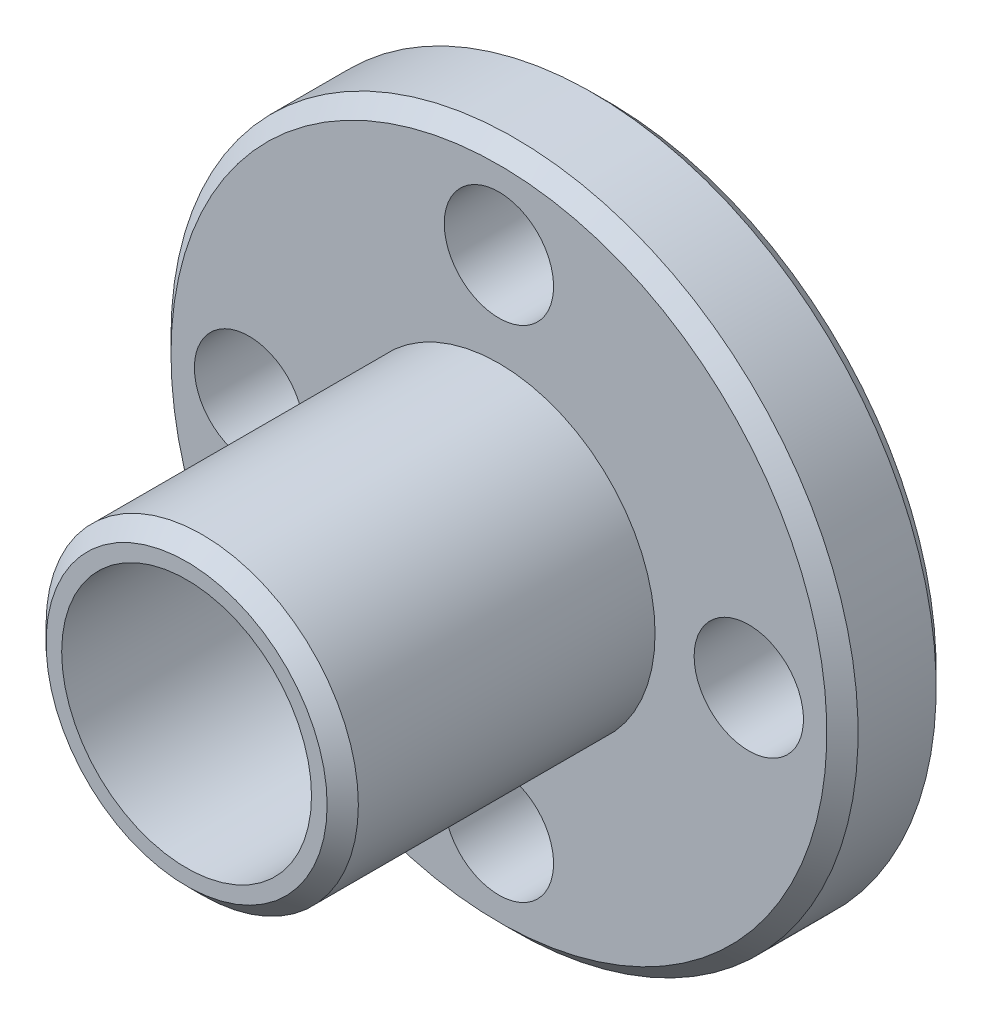
SolidWorks part; units mm, degrees
ref_plane "前视基准面" through (0, 0, 0) normal (0, 0, 1) x (1, 0, 0)
ref_plane "上视基准面" through (0, 0, 0) normal (0, 1, 0) x (1, 0, 0)
ref_plane "右视基准面" through (0, 0, 0) normal (1, 0, 0) x (0, 0, -1)
sketch "草图1" plane through (0, 0, 0) normal (0, 0, 1) x (1, 0, 0)
  circle A0 centre (0, 0) radius 5
  dimension "D1" = 10
extrude "凸台-拉伸1" add sketch "草图1" along normal mid plane 15
sketch "草图2" plane through (0, 0, -7.5) normal (0, 0, -1) x (-1, 0, 0)
  circle A0 centre (0, 0) radius 11
  dimension "D1" = 22
extrude "凸台-拉伸2" add sketch "草图2" against normal blind 3.5 from offset 1.5 offset against normal yes
sketch "草图3" plane through (0, 0, -7.5) normal (0, 0, -1) x (-1, 0, 0)
  circle A0 centre (0, 0) radius 4
  dimension "D1" = 8
extrude "切除-拉伸1" cut sketch "草图3" against normal through all
sketch "草图4" plane through (0, 0, -6) normal (0, 0, -1) x (-1, 0, 0)
  circle A0 centre (0, 0) radius 8 construction
  circle A1 centre (0, 8) radius 1.75
  circle A2 centre (8, 0) radius 1.75
  circle A3 centre (0, -8) radius 1.75
  circle A4 centre (-8, 0) radius 1.75
  dimension "D1" = 16
  dimension "D2" = 3.5
extrude "切除-拉伸2" cut sketch "草图4" against normal through all
chamfer "倒角1" distance 0.5 angle 45 4 edges at (5, 0, 7.5) (-11, 0, -2.5) (-11, 0, -6) (5, 0, -7.5)
